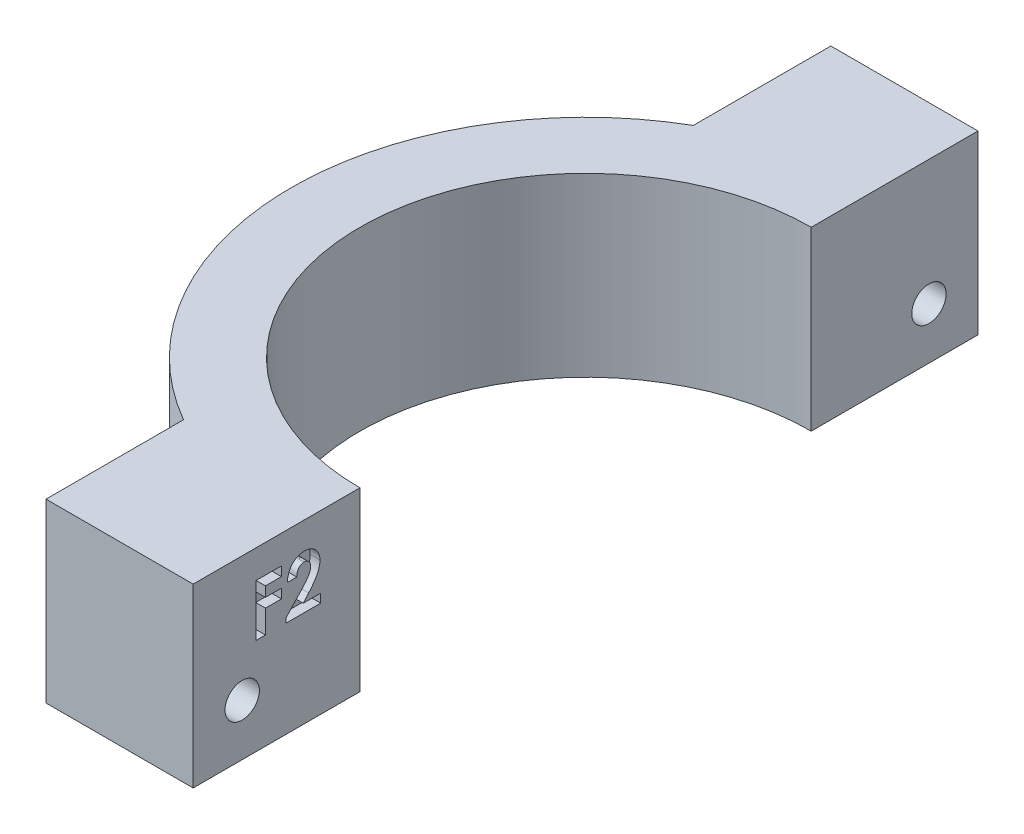
SolidWorks part; units mm, degrees
ref_plane "Front Plane" through (0, 0, 0) normal (0, 0, 1) x (1, 0, 0)
ref_plane "Top Plane" through (0, 0, 0) normal (0, 1, 0) x (1, 0, 0)
ref_plane "Right Plane" through (0, 0, 0) normal (1, 0, 0) x (0, 0, -1)
sketch "Sketch1" plane through (0, 0, 0) normal (0, 1, 0) x (1, 0, 0)
  line L0 (-46.9983, 32.5286) -> (-46.9983, -47.4714)
  line L1 (-46.9983, -47.4714) -> (-16.9983, -47.4714)
  line L2 (-16.9983, -47.4714) -> (-16.9983, -30.4714)
  line L3 (-46.9983, 32.5286) -> (-16.9983, 32.5286)
  line L4 (-16.9983, 32.5286) -> (-16.9983, 15.5286)
  line L5 (-31.9983, 32.5286) -> (-31.9983, 18.5093)
  line L6 (-31.9983, -47.4714) -> (-31.9983, -33.4522)
  arc A0 (-16.9983, 15.5286) -> (-16.9983, -30.4714) centre (-16.9983, -7.4714) ccw
  arc A1 (-16.9983, 22.5286) -> (-16.9983, -37.4714) centre (-16.9983, -7.4714) ccw
  dimension "D1" = 80
  dimension "D2" = 30
  dimension "D3" = 30
  dimension "D4" = 46
  dimension "D5" = 17
  dimension "D6" = 17
  dimension "D7" = 7
extrude "Boss-Extrude1" add sketch "Sketch1" along normal blind 18
sketch "Sketch2" plane through (-16.9983, 0, 0) normal (1, 0, 0) x (0, 0, -1)
  line L0 (-47.4714, 18) -> (-47.4714, 0) construction
  line L3 (32.5286, 18) -> (32.5286, 0) construction
  line L9 (-47.4714, 18) -> (-30.4714, 18) construction
  line L10 (32.5286, 18) -> (15.5286, 18) construction
  circle A0 centre (-42.4714, 5.25) radius 1.75
  circle A1 centre (27.5286, 5.25) radius 1.75
  dimension "D3" = 12.75
  dimension "D5" = 3.5
  dimension "D6" = 3.5
  dimension "D1" = 5
  dimension "D2" = 5
  dimension "D4" = 12.75
extrude "Cut-Extrude1" cut sketch "Sketch2" against normal through all
sketch "Sketch3" plane through (-16.9983, 0, 0) normal (1, 0, 0) x (0, 0, -1)
  text T0 "<b>F2</b>" font "Century Gothic" height in points 20
extrude "Cut-Extrude2" cut sketch "Sketch3" against normal blind 1
sketch "Sketch4" plane through (-31.9983, 0, 0) normal (-1, 0, 0) x (0, 0, 1)
  line L1 (-25.7357, 2.6291) -> (-24.3624, 5.4922)
  line L2 (-24.3624, 5.4922) -> (-26.1553, 8.1131)
  line L3 (-26.1553, 8.1131) -> (-29.3214, 7.8709)
  line L4 (-29.3214, 7.8709) -> (-30.6947, 5.0078)
  line L5 (-30.6947, 5.0078) -> (-28.9019, 2.3869)
  line L6 (-28.9019, 2.3869) -> (-25.7357, 2.6291)
  line L7 (45.1709, 3.5778) -> (45.2693, 6.7517)
  line L8 (45.2693, 6.7517) -> (42.5699, 8.4239)
  line L9 (42.5699, 8.4239) -> (39.772, 6.9222)
  line L10 (39.772, 6.9222) -> (39.6735, 3.7483)
  line L11 (39.6735, 3.7483) -> (42.373, 2.0761)
  line L12 (42.373, 2.0761) -> (45.1709, 3.5778)
  circle A0 centre (-27.5286, 5.25) radius 2.75 construction
  circle A1 centre (42.4714, 5.25) radius 2.75 construction
extrude "Cut-Extrude3" cut sketch "Sketch4" against normal blind 5
